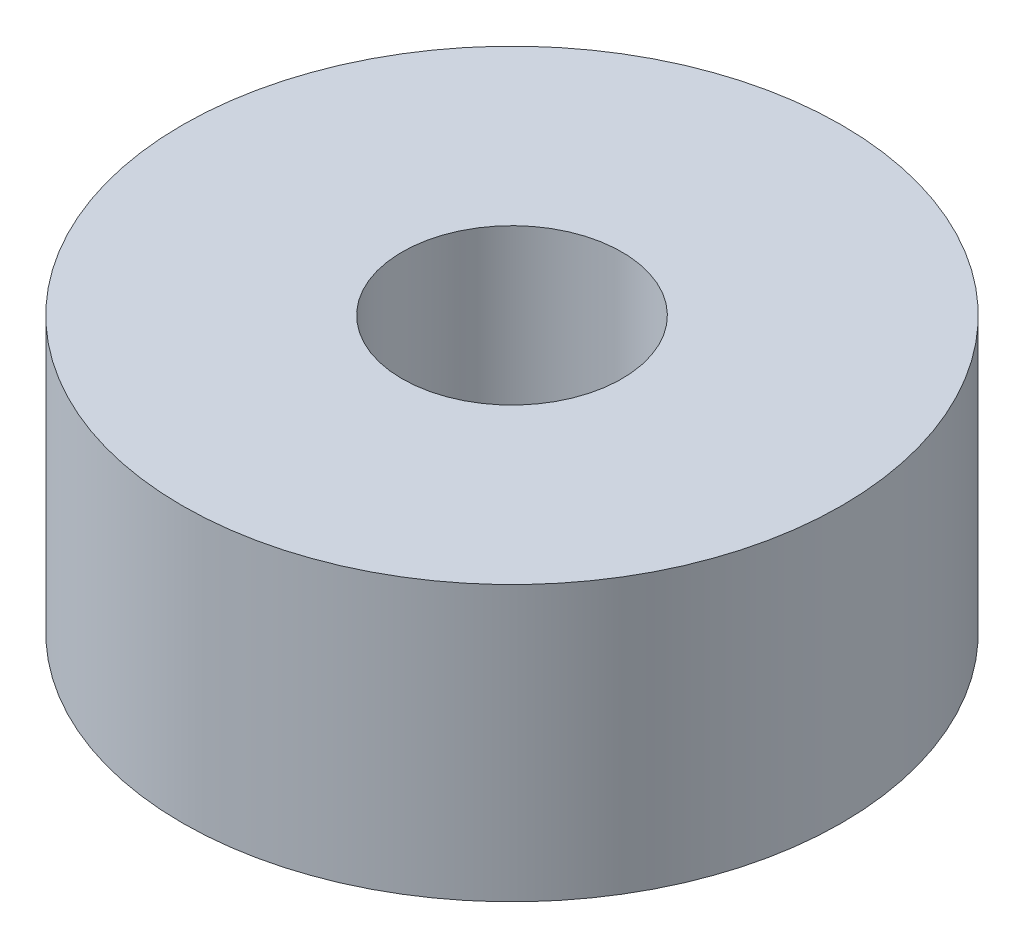
SolidWorks part; units mm, degrees
material "不锈钢 (铁素体)"
ref_plane "前视基准面" through (0, 0, 0) normal (0, 0, 1) x (1, 0, 0)
ref_plane "上视基准面" through (0, 0, 0) normal (0, 1, 0) x (1, 0, 0)
ref_plane "右视基准面" through (0, 0, 0) normal (1, 0, 0) x (0, 0, -1)
sketch "草图1" plane through (0, 0, 0) normal (0, 1, 0) x (1, 0, 0)
  circle A0 centre (0, 0) radius 1
  circle A1 centre (0, 0) radius 3
  dimension "D1" = 2
  dimension "D2" = 6
extrude "凸台-拉伸1" add sketch "草图1" along normal blind 2.5
